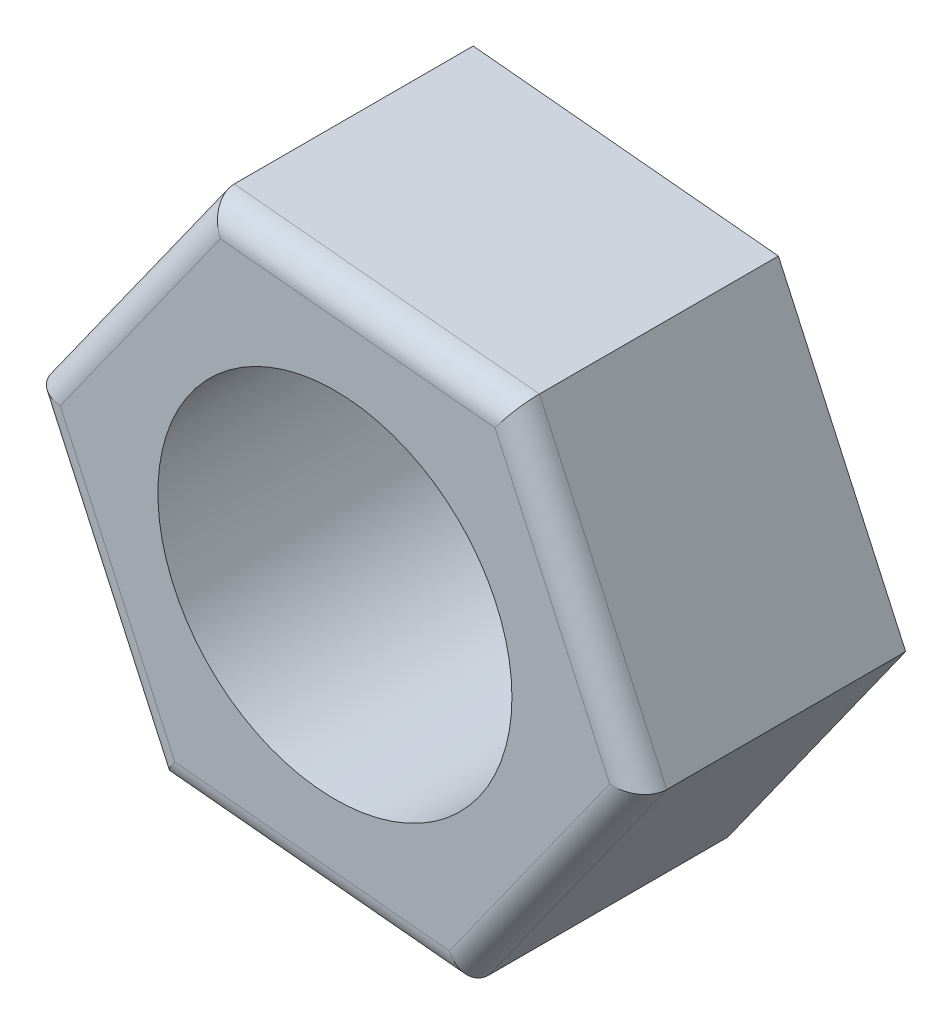
SolidWorks part; units mm, degrees
ref_plane "前视基准面" through (0, 0, 0) normal (0, 0, 1) x (1, 0, 0)
ref_plane "上视基准面" through (0, 0, 0) normal (0, 1, 0) x (1, 0, 0)
ref_plane "右视基准面" through (0, 0, 0) normal (1, 0, 0) x (0, 0, -1)
sketch "草图1" plane through (0, 0, 0) normal (0, 0, 1) x (1, 0, 0)
  line L1 (1.4377, -3.1517) -> (3.4483, -0.3307)
  line L2 (3.4483, -0.3307) -> (2.0105, 2.8209)
  line L3 (2.0105, 2.8209) -> (-1.4377, 3.1517)
  line L4 (-1.4377, 3.1517) -> (-3.4483, 0.3307)
  line L5 (-3.4483, 0.3307) -> (-2.0105, -2.8209)
  line L6 (-2.0105, -2.8209) -> (1.4377, -3.1517)
  circle A0 centre (0, 0) radius 3 construction
  circle A1 centre (0, 0) radius 2
  dimension "D1" = 4
  dimension "D2" = 6
extrude "凸台-拉伸1" add sketch "草图1" along normal blind 3
fillet "圆角1" radius 0.3 6 edges at (-0.2864, -2.9863, 3) (-2.7294, -1.2451, 3) (-2.443, 1.7412, 3) (0.2864, 2.9863, 3) (2.7294, 1.2451, 3) (2.443, -1.7412, 3)
